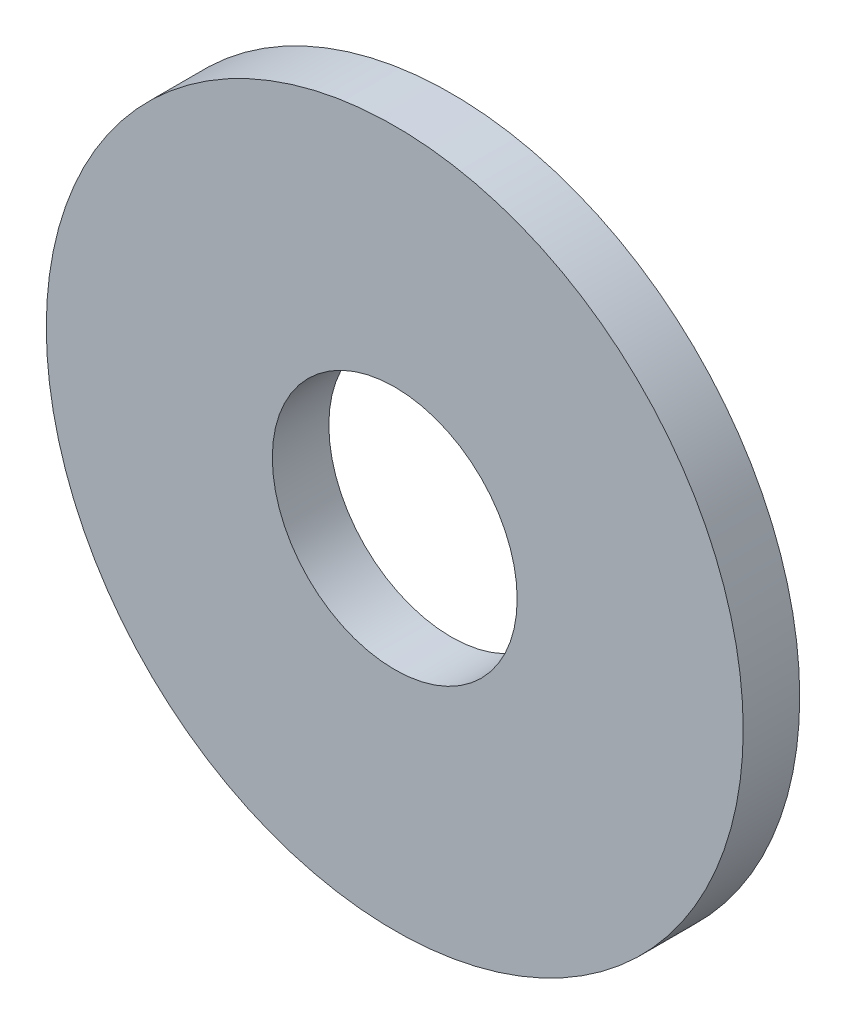
SolidWorks part; units mm, degrees
ref_plane "前视基准面" through (0, 0, 0) normal (0, 0, 1) x (1, 0, 0)
ref_plane "上视基准面" through (0, 0, 0) normal (0, 1, 0) x (1, 0, 0)
ref_plane "右视基准面" through (0, 0, 0) normal (1, 0, 0) x (0, 0, -1)
sketch "尺寸草图" plane through (0, 0, 0) normal (0, 0, 1) x (1, 0, 0)
  line L0 (0, 0) -> (3, 0) construction
  circle A0 centre (0, 0) radius 18.5
  circle A1 centre (0, 0) radius 6.5
  dimension "d2" = 37
  dimension "d1" = 13
  dimension "h" = 3
extrude "拉伸1" add sketch "尺寸草图" along normal blind 3
